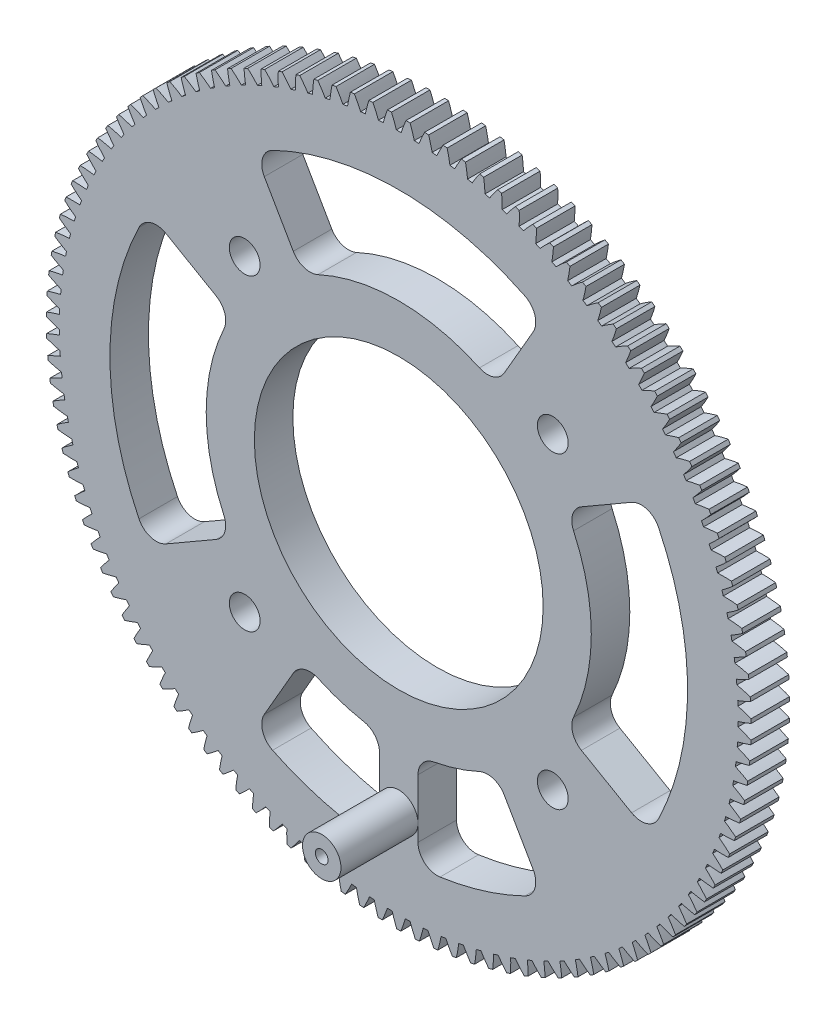
SolidWorks part; units mm, degrees
material "PMMA"
ref_plane "Front Plane" through (0, 0, 0) normal (0, 0, 1) x (1, 0, 0)
ref_plane "Top Plane" through (0, 0, 0) normal (0, 1, 0) x (1, 0, 0)
ref_plane "Right Plane" through (0, 0, 0) normal (1, 0, 0) x (0, 0, -1)
sketch "Sketch1" plane through (0, 0, 0) normal (1, 0, 0) x (0, 0, -1)
  line L1 (0, 0) -> (10, 0)
  line L2 (0, 0) -> (0, 91.5)
  line L3 (0, 91.5) -> (10, 91.5)
  line L4 (10, 0) -> (10, 91.5)
  dimension "D1" = 10
  dimension "D2" = 91.5
revolve "Revolve1" add sketch "Sketch1" angle 360 about L1
sketch "Sketch2" plane through (0, 0, 0) normal (0, 0, 1) x (1, 0, 0)
  line L0 (0, 0) -> (0, 130) construction
  line L1 (0, 0) -> (3.403, 129.9555) construction
  line L2 (2.3559, 89.9692) -> (1.2709, 89.9692) construction
  circle A0 centre (0, 0) radius 91.5255 construction
  circle A1 centre (0, 0) radius 90 construction
  circle A2 centre (0, 0) radius 88.124 construction
  circle A3 centre (0, 0) radius 84.577 construction
  arc A5 (1.9026, 91.5057) -> (-1.9026, 91.5057) centre (0, 0) ccw
  arc A9 (0.618, 88.1218) -> (-0.618, 88.1218) centre (0, 0) ccw
  arc A10 (1.9026, 91.5057) -> (0.618, 88.1218) centre (34.8739, 77.0525) ccw
  arc A11 (-1.9026, 91.5057) -> (-0.618, 88.1218) centre (-34.8739, 77.0525) cw
  point P12 (0, 88.124)
  point P13 (0, 91.5255)
  dimension "D1" = 183.051
  dimension "D2" = 180
  dimension "D3" = 176.248
  dimension "D4" = 169.154
  dimension "D7" = 36
  dimension "D5" = 1.5
  dimension "D6" = 130
  dimension "D8" = 1.085
extrude "Cut-Extrude1" cut sketch "Sketch2" against normal through all
pattern_circular "CirPattern1" count 119 over 360 about axis through (0, 0, 0) along (0, 0, 1) of "Cut-Extrude1"
sketch "Sketch3" plane through (0, 0, 0) normal (0, 0, 1) x (1, 0, 0)
  line L1 (-40, -40) -> (40, -40) construction
  line L2 (-40, -40) -> (-40, 40) construction
  line L3 (-40, 40) -> (40, 40) construction
  line L4 (40, -40) -> (40, 40) construction
  line L5 (-40, -40) -> (40, 40) construction
  line L6 (-40, 40) -> (40, -40) construction
  circle A0 centre (0, 0) radius 37.5
  circle A1 centre (0, 0) radius 57.5 construction
  circle A3 centre (40, 40) radius 4
  circle A4 centre (-40, 40) radius 4
  circle A5 centre (-40, -40) radius 4
  circle A6 centre (40, -40) radius 4
  dimension "D1" = 75
  dimension "D2" = 115
  dimension "D5" = 8
  dimension "D4" = 80
extrude "Cut-Extrude2" cut sketch "Sketch3" against normal through all
sketch "Sketch8" plane through (0, 0, 0) normal (0, 0, 1) x (1, 0, 0)
  line L0 (-1000, 0) -> (49000, 0) construction
  line L1 (0, -1000) -> (0, 49000) construction
  line L2 (0, 0) -> (-64.9519, -37.5) construction
  line L3 (0, 0) -> (-64.9519, 37.5) construction
  line L4 (-64.9519, -37.5) -> (-43.3013, -25)
  line L5 (-43.3013, 25) -> (-64.9519, 37.5)
  arc A0 (-64.9519, -37.5) -> (-64.9519, 37.5) centre (0, 0) cw
  arc A1 (-43.3013, -25) -> (-43.3013, 25) centre (0, 0) cw
  dimension "D4" = 50
  dimension "D1" = 75
  dimension "D2" = 30
  dimension "D3" = 30
extrude "Cut-Extrude3" cut sketch "Sketch8" against normal through all
fillet "Fillet1" radius 5 4 edges at (-64.9519, 37.5, -5) (-43.3013, 25, -5) (-43.3013, -25, -5) (-64.9519, -37.5, -5)
pattern_circular "CirPattern2" count 4 over 360 about axis through (0, 0, 0) along (0, 0, 1) of "Fillet1", "Cut-Extrude3"
sketch "Sketch5" plane through (0, 0, -10) normal (0, 0, -1) x (-1, 0, 0)
  circle A0 centre (0, -65) radius 5
  dimension "D1" = 10
  dimension "D2" = 65
extrude "Boss-Extrude2" add sketch "Sketch5" against normal blind 30
hole_wizard "M4 Tapped Hole1" positions "Sketch6" profile "Sketch7" tap size "M4" standard "ISO"
sketch "Sketch6" plane through (0, 0, 20) normal (0, 0, 1) x (1, 0, 0)
  point P0 (0, -65)
sketch "Sketch7" plane through (0, -65, 20) normal (1, 0, 0) x (0, -1, 0)
  line L0 (0, 0) -> (0, 21.0914)
  line L1 (0, 21.0914) -> (1.65, 20.1)
  line L2 (1.65, 20.1) -> (1.65, 0)
  line L5 (1.65, 0) -> (0, 0)
  line L10 (0, 21.0914) -> (-1.65, 20.1) construction
  line L11 (0, -6.35) -> (0, 107.95) construction
  dimension "Tap Drill Dia." = 3.3
  dimension "Tap Drill Depth" = 20.1
  dimension "Drill Angle" = 118
cosmetic thread "Hole Thread1" parameters "D1"=18, "D2"=4
sketch "Sketch9" plane through (0, 0, -10) normal (0, 0, -1) x (-1, 0, 0)
  line L1 (-5, -48) -> (5, -48)
  line L2 (-5, -48) -> (-5, -78)
  line L3 (-5, -78) -> (5, -78)
  line L4 (5, -48) -> (5, -78)
  circle A1 centre (0, -65) radius 5 construction
  circle A2 centre (0, 0) radius 37.5 construction
  dimension "D1" = 30
  dimension "D2" = 48
extrude "Boss-Extrude3" add sketch "Sketch9" against normal blind 10
fillet "Fillet2" radius 5 4 edges at (-5, -74.8331, -5) (5, -74.8331, -5) (5, -49.7494, -5) (-5, -49.7494, -5)
